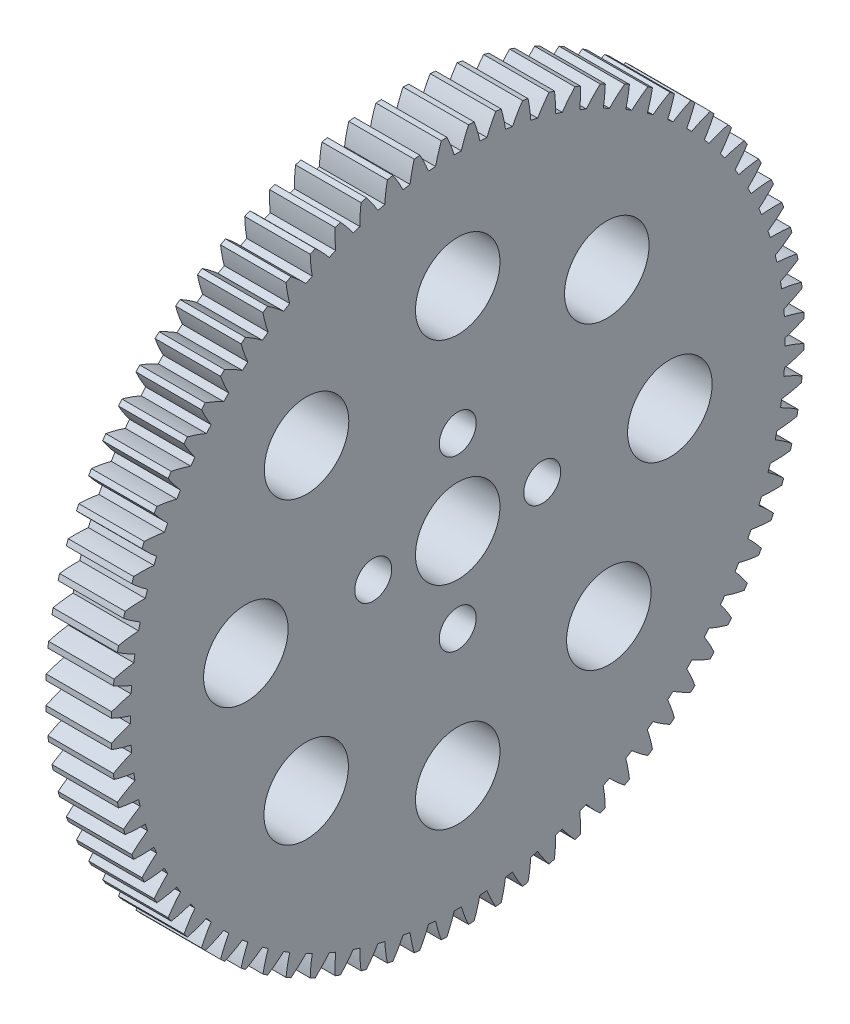
SolidWorks part; units mm, degrees
material "2024 Alloy"
ref_plane "Front Plane" through (0, 0, 0) normal (0, 0, 1) x (1, 0, 0)
ref_plane "Top Plane" through (0, 0, 0) normal (0, 1, 0) x (1, 0, 0)
ref_plane "Right Plane" through (0, 0, 0) normal (1, 0, 0) x (0, 0, -1)
ref_plane "Plane1" through (0, 0, 0) normal (-1, 0, 0) x (0, -1, 0)
sketch "Sketch1" plane through (0, 0, 0) normal (-1, 0, 0) x (0, -1, 0)
  circle A0 centre (0, 0) radius 4
  circle A1 centre (0, 8) radius 1.75
  circle A2 centre (-20.084, 0) radius 4
  circle A3 centre (20.0633, 0) radius 4
  circle A4 centre (0, -20.084) radius 4
  circle A5 centre (0, 20.0633) radius 4
  circle A6 centre (-14.3663, -14.1126) radius 4
  circle A7 centre (14.142, -14.3069) radius 4
  circle A8 centre (14.1351, 14.3483) radius 4
  circle A9 centre (-14.1597, 14.315) radius 4
  circle A10 centre (-8, 0) radius 1.75
  circle A11 centre (8, 0) radius 1.75
  circle A12 centre (0, -8) radius 1.75
  arc A13 (-32.5405, -4.1179) -> (-30.6681, -4.5175) centre (-28.9403, 8.1654) ccw
  arc A14 (-30.6681, -4.5175) -> (-30.563, -5.1806) centre (0, 0) ccw
  arc A15 (-30.563, -5.1806) -> (-32.2203, -6.1392) centre (-25.0006, -16.7088) ccw
  arc A16 (-32.2203, -6.1392) -> (-32.1171, -6.6583) centre (0, 0) ccw
  arc A17 (-32.1171, -6.6583) -> (-30.2191, -6.9097) centre (-29.4917, 5.8696) ccw
  arc A18 (-30.2191, -6.9097) -> (-30.0624, -7.5626) centre (0, 0) ccw
  arc A19 (-30.0624, -7.5626) -> (-31.6393, -8.6483) centre (-23.6126, -18.6188) ccw
  arc A20 (-31.6393, -8.6483) -> (-31.4957, -9.1576) centre (0, 0) ccw
  arc A21 (-31.4957, -9.1576) -> (-29.5838, -9.2594) centre (-29.8613, 3.5376) ccw
  arc A22 (-29.5838, -9.2594) -> (-29.3763, -9.8979) centre (0, 0) ccw
  arc A23 (-29.3763, -9.8979) -> (-30.8633, -11.104) centre (-22.079, -20.414) ccw
  arc A24 (-30.8633, -11.104) -> (-30.6801, -11.6005) centre (0, 0) ccw
  arc A25 (-30.6801, -11.6005) -> (-28.7661, -11.552) centre (-30.0469, 1.1838) ccw
  arc A26 (-28.7661, -11.552) -> (-28.5092, -12.1723) centre (0, 0) ccw
  arc A27 (-28.5092, -12.1723) -> (-29.8969, -13.4913) centre (-20.4093, -22.0834) ccw
  arc A28 (-29.8969, -13.4913) -> (-29.6753, -13.9719) centre (0, 0) ccw
  arc A29 (-29.6753, -13.9719) -> (-27.7711, -13.7733) centre (-30.0471, -1.1773) ccw
  arc A30 (-27.7711, -13.7733) -> (-27.4663, -14.3715) centre (0, 0) ccw
  arc A31 (-27.4663, -14.3715) -> (-28.7462, -15.7954) centre (-18.6137, -23.6166) ccw
  arc A32 (-28.7462, -15.7954) -> (-28.4876, -16.2571) centre (0, 0) ccw
  arc A33 (-28.4876, -16.2571) -> (-26.6048, -15.9097) centre (-29.8621, -3.5311) ccw
  arc A34 (-26.6048, -15.9097) -> (-26.254, -16.4822) centre (0, 0) ccw
  arc A35 (-26.254, -16.4822) -> (-27.4183, -18.0021) centre (-16.7034, -25.0042) ccw
  arc A36 (-27.4183, -18.0021) -> (-27.1243, -18.4421) centre (0, 0) ccw
  arc A37 (-27.1243, -18.4421) -> (-25.2746, -17.9481) centre (-29.493, -5.8632) ccw
  arc A38 (-25.2746, -17.9481) -> (-24.8799, -18.4913) centre (0, 0) ccw
  arc A39 (-24.8799, -18.4913) -> (-25.9214, -20.0978) centre (-14.6901, -26.2377) ccw
  arc A40 (-25.9214, -20.0978) -> (-25.5937, -20.5134) centre (0, 0) ccw
  arc A41 (-25.5937, -20.5134) -> (-23.7885, -19.8758) centre (-28.9421, -8.1591) ccw
  arc A42 (-23.7885, -19.8758) -> (-23.3524, -20.3863) centre (0, 0) ccw
  arc A43 (-23.3524, -20.3863) -> (-24.2646, -22.0696) centre (-12.5862, -27.3094) ccw
  arc A44 (-24.2646, -22.0696) -> (-23.9054, -22.4582) centre (0, 0) ccw
  arc A45 (-23.9054, -22.4582) -> (-22.1557, -21.6809) centre (-28.2127, -10.4047) ccw
  arc A46 (-22.1557, -21.6809) -> (-21.6809, -22.1557) centre (0, 0) ccw
  arc A47 (-21.6809, -22.1557) -> (-22.4582, -23.9054) centre (-10.4047, -28.2127) ccw
  arc A48 (-22.4582, -23.9054) -> (-22.0696, -24.2646) centre (0, 0) ccw
  arc A49 (-22.0696, -24.2646) -> (-20.3863, -23.3524) centre (-27.3094, -12.5862) ccw
  arc A50 (-20.3863, -23.3524) -> (-19.8758, -23.7885) centre (0, 0) ccw
  arc A51 (-19.8758, -23.7885) -> (-20.5134, -25.5937) centre (-8.1591, -28.9421) ccw
  arc A52 (-20.5134, -25.5937) -> (-20.0978, -25.9214) centre (0, 0) ccw
  arc A53 (-20.0978, -25.9214) -> (-18.4913, -24.8799) centre (-26.2377, -14.6901) ccw
  arc A54 (-18.4913, -24.8799) -> (-17.9481, -25.2746) centre (0, 0) ccw
  arc A55 (-17.9481, -25.2746) -> (-18.4421, -27.1243) centre (-5.8632, -29.493) ccw
  arc A56 (-18.4421, -27.1243) -> (-18.0021, -27.4183) centre (0, 0) ccw
  arc A57 (-18.0021, -27.4183) -> (-16.4822, -26.254) centre (-25.0042, -16.7034) ccw
  arc A58 (-16.4822, -26.254) -> (-15.9097, -26.6048) centre (0, 0) ccw
  arc A59 (-15.9097, -26.6048) -> (-16.2571, -28.4876) centre (-3.5311, -29.8621) ccw
  arc A60 (-16.2571, -28.4876) -> (-15.7954, -28.7462) centre (0, 0) ccw
  arc A61 (-15.7954, -28.7462) -> (-14.3715, -27.4663) centre (-23.6166, -18.6137) ccw
  arc A62 (-14.3715, -27.4663) -> (-13.7733, -27.7711) centre (0, 0) ccw
  arc A63 (-13.7733, -27.7711) -> (-13.9719, -29.6753) centre (-1.1773, -30.0471) ccw
  arc A64 (-13.9719, -29.6753) -> (-13.4913, -29.8969) centre (0, 0) ccw
  arc A65 (-13.4913, -29.8969) -> (-12.1723, -28.5092) centre (-22.0834, -20.4093) ccw
  arc A66 (-12.1723, -28.5092) -> (-11.552, -28.7661) centre (0, 0) ccw
  arc A67 (-11.552, -28.7661) -> (-11.6005, -30.6801) centre (1.1838, -30.0469) ccw
  arc A68 (-11.6005, -30.6801) -> (-11.104, -30.8633) centre (0, 0) ccw
  arc A69 (-11.104, -30.8633) -> (-9.8979, -29.3763) centre (-20.414, -22.079) ccw
  arc A70 (-9.8979, -29.3763) -> (-9.2594, -29.5838) centre (0, 0) ccw
  arc A71 (-9.2594, -29.5838) -> (-9.1576, -31.4957) centre (3.5376, -29.8613) ccw
  arc A72 (-9.1576, -31.4957) -> (-8.6483, -31.6393) centre (0, 0) ccw
  arc A73 (-8.6483, -31.6393) -> (-7.5626, -30.0624) centre (-18.6188, -23.6126) ccw
  arc A74 (-7.5626, -30.0624) -> (-6.9097, -30.2191) centre (0, 0) ccw
  arc A75 (-6.9097, -30.2191) -> (-6.6583, -32.1171) centre (5.8696, -29.4917) ccw
  arc A76 (-6.6583, -32.1171) -> (-6.1392, -32.2203) centre (0, 0) ccw
  arc A77 (-6.1392, -32.2203) -> (-5.1806, -30.563) centre (-16.7088, -25.0006) ccw
  arc A78 (-5.1806, -30.563) -> (-4.5175, -30.6681) centre (0, 0) ccw
  arc A79 (-4.5175, -30.6681) -> (-4.1179, -32.5405) centre (8.1654, -28.9403) ccw
  arc A80 (-4.1179, -32.5405) -> (-3.5923, -32.6027) centre (0, 0) ccw
  arc A81 (-3.5923, -32.6027) -> (-2.7667, -30.8753) centre (-14.6958, -26.2345) ccw
  arc A82 (-2.7667, -30.8753) -> (-2.0973, -30.928) centre (0, 0) ccw
  arc A83 (-2.0973, -30.928) -> (-1.5521, -32.7633) centre (10.4109, -28.2104) ccw
  arc A84 (-1.5521, -32.7633) -> (-1.0233, -32.784) centre (0, 0) ccw
  arc A85 (-1.0233, -32.784) -> (-0.3357, -30.9972) centre (-12.5921, -27.3066) ccw
  arc A86 (-0.3357, -30.9972) -> (0.3357, -30.9972) centre (0, 0) ccw
  arc A87 (0.3357, -30.9972) -> (1.0233, -32.784) centre (12.5921, -27.3066) ccw
  arc A88 (1.0233, -32.784) -> (1.5521, -32.7633) centre (0, 0) ccw
  arc A89 (1.5521, -32.7633) -> (2.0973, -30.928) centre (-10.4109, -28.2104) ccw
  arc A90 (2.0973, -30.928) -> (2.7667, -30.8753) centre (0, 0) ccw
  arc A91 (2.7667, -30.8753) -> (3.5923, -32.6027) centre (14.6958, -26.2345) ccw
  arc A92 (3.5923, -32.6027) -> (4.1179, -32.5405) centre (0, 0) ccw
  arc A93 (4.1179, -32.5405) -> (4.5175, -30.6681) centre (-8.1654, -28.9403) ccw
  arc A94 (4.5175, -30.6681) -> (5.1806, -30.563) centre (0, 0) ccw
  arc A95 (5.1806, -30.563) -> (6.1392, -32.2203) centre (16.7088, -25.0006) ccw
  arc A96 (6.1392, -32.2203) -> (6.6583, -32.1171) centre (0, 0) ccw
  arc A97 (6.6583, -32.1171) -> (6.9097, -30.2191) centre (-5.8696, -29.4917) ccw
  arc A98 (6.9097, -30.2191) -> (7.5626, -30.0624) centre (0, 0) ccw
  arc A99 (7.5626, -30.0624) -> (8.6483, -31.6393) centre (18.6188, -23.6126) ccw
  arc A100 (8.6483, -31.6393) -> (9.1576, -31.4957) centre (0, 0) ccw
  arc A101 (9.1576, -31.4957) -> (9.2594, -29.5838) centre (-3.5376, -29.8613) ccw
  arc A102 (9.2594, -29.5838) -> (9.8979, -29.3763) centre (0, 0) ccw
  arc A103 (9.8979, -29.3763) -> (11.104, -30.8633) centre (20.414, -22.079) ccw
  arc A104 (11.104, -30.8633) -> (11.6005, -30.6801) centre (0, 0) ccw
  arc A105 (11.6005, -30.6801) -> (11.552, -28.7661) centre (-1.1838, -30.0469) ccw
  arc A106 (11.552, -28.7661) -> (12.1723, -28.5092) centre (0, 0) ccw
  arc A107 (12.1723, -28.5092) -> (13.4913, -29.8969) centre (22.0834, -20.4093) ccw
  arc A108 (13.4913, -29.8969) -> (13.9719, -29.6753) centre (0, 0) ccw
  arc A109 (13.9719, -29.6753) -> (13.7733, -27.7711) centre (1.1773, -30.0471) ccw
  arc A110 (13.7733, -27.7711) -> (14.3715, -27.4663) centre (0, 0) ccw
  arc A111 (14.3715, -27.4663) -> (15.7954, -28.7462) centre (23.6166, -18.6137) ccw
  arc A112 (15.7954, -28.7462) -> (16.2571, -28.4876) centre (0, 0) ccw
  arc A113 (16.2571, -28.4876) -> (15.9097, -26.6048) centre (3.5311, -29.8621) ccw
  arc A114 (15.9097, -26.6048) -> (16.4822, -26.254) centre (0, 0) ccw
  arc A115 (16.4822, -26.254) -> (18.0021, -27.4183) centre (25.0042, -16.7034) ccw
  arc A116 (18.0021, -27.4183) -> (18.4421, -27.1243) centre (0, 0) ccw
  arc A117 (18.4421, -27.1243) -> (17.9481, -25.2746) centre (5.8632, -29.493) ccw
  arc A118 (17.9481, -25.2746) -> (18.4913, -24.8799) centre (0, 0) ccw
  arc A119 (18.4913, -24.8799) -> (20.0978, -25.9214) centre (26.2377, -14.6901) ccw
  arc A120 (20.0978, -25.9214) -> (20.5134, -25.5937) centre (0, 0) ccw
  arc A121 (20.5134, -25.5937) -> (19.8758, -23.7885) centre (8.1591, -28.9421) ccw
  arc A122 (19.8758, -23.7885) -> (20.3863, -23.3524) centre (0, 0) ccw
  arc A123 (20.3863, -23.3524) -> (22.0696, -24.2646) centre (27.3094, -12.5862) ccw
  arc A124 (22.0696, -24.2646) -> (22.4582, -23.9054) centre (0, 0) ccw
  arc A125 (22.4582, -23.9054) -> (21.6809, -22.1557) centre (10.4047, -28.2127) ccw
  arc A126 (21.6809, -22.1557) -> (22.1557, -21.6809) centre (0, 0) ccw
  arc A127 (22.1557, -21.6809) -> (23.9054, -22.4582) centre (28.2127, -10.4047) ccw
  arc A128 (23.9054, -22.4582) -> (24.2646, -22.0696) centre (0, 0) ccw
  arc A129 (24.2646, -22.0696) -> (23.3524, -20.3863) centre (12.5862, -27.3094) ccw
  arc A130 (23.3524, -20.3863) -> (23.7885, -19.8758) centre (0, 0) ccw
  arc A131 (23.7885, -19.8758) -> (25.5937, -20.5134) centre (28.9421, -8.1591) ccw
  arc A132 (25.5937, -20.5134) -> (25.9214, -20.0978) centre (0, 0) ccw
  arc A133 (25.9214, -20.0978) -> (24.8799, -18.4913) centre (14.6901, -26.2377) ccw
  arc A134 (24.8799, -18.4913) -> (25.2746, -17.9481) centre (0, 0) ccw
  arc A135 (25.2746, -17.9481) -> (27.1243, -18.4421) centre (29.493, -5.8632) ccw
  arc A136 (27.1243, -18.4421) -> (27.4183, -18.0021) centre (0, 0) ccw
  arc A137 (27.4183, -18.0021) -> (26.254, -16.4822) centre (16.7034, -25.0042) ccw
  arc A138 (26.254, -16.4822) -> (26.6048, -15.9097) centre (0, 0) ccw
  arc A139 (26.6048, -15.9097) -> (28.4876, -16.2571) centre (29.8621, -3.5311) ccw
  arc A140 (28.4876, -16.2571) -> (28.7462, -15.7954) centre (0, 0) ccw
  arc A141 (28.7462, -15.7954) -> (27.4663, -14.3715) centre (18.6137, -23.6166) ccw
  arc A142 (27.4663, -14.3715) -> (27.7711, -13.7733) centre (0, 0) ccw
  arc A143 (27.7711, -13.7733) -> (29.6753, -13.9719) centre (30.0471, -1.1773) ccw
  arc A144 (29.6753, -13.9719) -> (29.8969, -13.4913) centre (0, 0) ccw
  arc A145 (29.8969, -13.4913) -> (28.5092, -12.1723) centre (20.4093, -22.0834) ccw
  arc A146 (28.5092, -12.1723) -> (28.7661, -11.552) centre (0, 0) ccw
  arc A147 (28.7661, -11.552) -> (30.6801, -11.6005) centre (30.0469, 1.1838) ccw
  arc A148 (30.6801, -11.6005) -> (30.8633, -11.104) centre (0, 0) ccw
  arc A149 (30.8633, -11.104) -> (29.3763, -9.8979) centre (22.079, -20.414) ccw
  arc A150 (29.3763, -9.8979) -> (29.5838, -9.2594) centre (0, 0) ccw
  arc A151 (29.5838, -9.2594) -> (31.4957, -9.1576) centre (29.8613, 3.5376) ccw
  arc A152 (31.4957, -9.1576) -> (31.6393, -8.6483) centre (0, 0) ccw
  arc A153 (31.6393, -8.6483) -> (30.0624, -7.5626) centre (23.6126, -18.6188) ccw
  arc A154 (30.0624, -7.5626) -> (30.2191, -6.9097) centre (0, 0) ccw
  arc A155 (30.2191, -6.9097) -> (32.1171, -6.6583) centre (29.4917, 5.8696) ccw
  arc A156 (32.1171, -6.6583) -> (32.2203, -6.1392) centre (0, 0) ccw
  arc A157 (32.2203, -6.1392) -> (30.563, -5.1806) centre (25.0006, -16.7088) ccw
  arc A158 (30.563, -5.1806) -> (30.6681, -4.5175) centre (0, 0) ccw
  arc A159 (30.6681, -4.5175) -> (32.5405, -4.1179) centre (28.9403, 8.1654) ccw
  arc A160 (32.5405, -4.1179) -> (32.6027, -3.5923) centre (0, 0) ccw
  arc A161 (32.6027, -3.5923) -> (30.8753, -2.7667) centre (26.2345, -14.6958) ccw
  arc A162 (30.8753, -2.7667) -> (30.928, -2.0973) centre (0, 0) ccw
  arc A163 (30.928, -2.0973) -> (32.7633, -1.5521) centre (28.2104, 10.4109) ccw
  arc A164 (32.7633, -1.5521) -> (32.784, -1.0233) centre (0, 0) ccw
  arc A165 (32.784, -1.0233) -> (30.9972, -0.3357) centre (27.3066, -12.5921) ccw
  arc A166 (30.9972, -0.3357) -> (30.9972, 0.3357) centre (0, 0) ccw
  arc A167 (30.9972, 0.3357) -> (32.784, 1.0233) centre (27.3066, 12.5921) ccw
  arc A168 (32.784, 1.0233) -> (32.7633, 1.5521) centre (0, 0) ccw
  arc A169 (32.7633, 1.5521) -> (30.928, 2.0973) centre (28.2104, -10.4109) ccw
  arc A170 (30.928, 2.0973) -> (30.8753, 2.7667) centre (0, 0) ccw
  arc A171 (30.8753, 2.7667) -> (32.6027, 3.5923) centre (26.2345, 14.6958) ccw
  arc A172 (32.6027, 3.5923) -> (32.5405, 4.1179) centre (0, 0) ccw
  arc A173 (32.5405, 4.1179) -> (30.6681, 4.5175) centre (28.9403, -8.1654) ccw
  arc A174 (30.6681, 4.5175) -> (30.563, 5.1806) centre (0, 0) ccw
  arc A175 (30.563, 5.1806) -> (32.2203, 6.1392) centre (25.0006, 16.7088) ccw
  arc A176 (32.2203, 6.1392) -> (32.1171, 6.6583) centre (0, 0) ccw
  arc A177 (32.1171, 6.6583) -> (30.2191, 6.9097) centre (29.4917, -5.8696) ccw
  arc A178 (30.2191, 6.9097) -> (30.0624, 7.5626) centre (0, 0) ccw
  arc A179 (30.0624, 7.5626) -> (31.6393, 8.6483) centre (23.6126, 18.6188) ccw
  arc A180 (31.6393, 8.6483) -> (31.4957, 9.1576) centre (0, 0) ccw
  arc A181 (31.4957, 9.1576) -> (29.5838, 9.2594) centre (29.8613, -3.5376) ccw
  arc A182 (29.5838, 9.2594) -> (29.3763, 9.8979) centre (0, 0) ccw
  arc A183 (29.3763, 9.8979) -> (30.8633, 11.104) centre (22.079, 20.414) ccw
  arc A184 (30.8633, 11.104) -> (30.6801, 11.6005) centre (0, 0) ccw
  arc A185 (30.6801, 11.6005) -> (28.7661, 11.552) centre (30.0469, -1.1838) ccw
  arc A186 (28.7661, 11.552) -> (28.5092, 12.1723) centre (0, 0) ccw
  arc A187 (28.5092, 12.1723) -> (29.8969, 13.4913) centre (20.4093, 22.0834) ccw
  arc A188 (29.8969, 13.4913) -> (29.6753, 13.9719) centre (0, 0) ccw
  arc A189 (29.6753, 13.9719) -> (27.7711, 13.7733) centre (30.0471, 1.1773) ccw
  arc A190 (27.7711, 13.7733) -> (27.4663, 14.3715) centre (0, 0) ccw
  arc A191 (27.4663, 14.3715) -> (28.7462, 15.7954) centre (18.6137, 23.6166) ccw
  arc A192 (28.7462, 15.7954) -> (28.4876, 16.2571) centre (0, 0) ccw
  arc A193 (28.4876, 16.2571) -> (26.6048, 15.9097) centre (29.8621, 3.5311) ccw
  arc A194 (26.6048, 15.9097) -> (26.254, 16.4822) centre (0, 0) ccw
  arc A195 (26.254, 16.4822) -> (27.4183, 18.0021) centre (16.7034, 25.0042) ccw
  arc A196 (27.4183, 18.0021) -> (27.1243, 18.4421) centre (0, 0) ccw
  arc A197 (27.1243, 18.4421) -> (25.2746, 17.9481) centre (29.493, 5.8632) ccw
  arc A198 (25.2746, 17.9481) -> (24.8799, 18.4913) centre (0, 0) ccw
  arc A199 (24.8799, 18.4913) -> (25.9214, 20.0978) centre (14.6901, 26.2377) ccw
  arc A200 (25.9214, 20.0978) -> (25.5937, 20.5134) centre (0, 0) ccw
  arc A201 (25.5937, 20.5134) -> (23.7885, 19.8758) centre (28.9421, 8.1591) ccw
  arc A202 (23.7885, 19.8758) -> (23.3524, 20.3863) centre (0, 0) ccw
  arc A203 (23.3524, 20.3863) -> (24.2646, 22.0696) centre (12.5862, 27.3094) ccw
  arc A204 (24.2646, 22.0696) -> (23.9054, 22.4582) centre (0, 0) ccw
  arc A205 (23.9054, 22.4582) -> (22.1557, 21.6809) centre (28.2127, 10.4047) ccw
  arc A206 (22.1557, 21.6809) -> (21.6809, 22.1557) centre (0, 0) ccw
  arc A207 (21.6809, 22.1557) -> (22.4582, 23.9054) centre (10.4047, 28.2127) ccw
  arc A208 (22.4582, 23.9054) -> (22.0696, 24.2646) centre (0, 0) ccw
  arc A209 (22.0696, 24.2646) -> (20.3863, 23.3524) centre (27.3094, 12.5862) ccw
  arc A210 (20.3863, 23.3524) -> (19.8758, 23.7885) centre (0, 0) ccw
  arc A211 (19.8758, 23.7885) -> (20.5134, 25.5937) centre (8.1591, 28.9421) ccw
  arc A212 (20.5134, 25.5937) -> (20.0978, 25.9214) centre (0, 0) ccw
  arc A213 (20.0978, 25.9214) -> (18.4913, 24.8799) centre (26.2377, 14.6901) ccw
  arc A214 (18.4913, 24.8799) -> (17.9481, 25.2746) centre (0, 0) ccw
  arc A215 (17.9481, 25.2746) -> (18.4421, 27.1243) centre (5.8632, 29.493) ccw
  arc A216 (18.4421, 27.1243) -> (18.0021, 27.4183) centre (0, 0) ccw
  arc A217 (18.0021, 27.4183) -> (16.4822, 26.254) centre (25.0042, 16.7034) ccw
  arc A218 (16.4822, 26.254) -> (15.9097, 26.6048) centre (0, 0) ccw
  arc A219 (15.9097, 26.6048) -> (16.2571, 28.4876) centre (3.5311, 29.8621) ccw
  arc A220 (16.2571, 28.4876) -> (15.7954, 28.7462) centre (0, 0) ccw
  arc A221 (15.7954, 28.7462) -> (14.3715, 27.4663) centre (23.6166, 18.6137) ccw
  arc A222 (14.3715, 27.4663) -> (13.7733, 27.7711) centre (0, 0) ccw
  arc A223 (13.7733, 27.7711) -> (13.9719, 29.6753) centre (1.1773, 30.0471) ccw
  arc A224 (13.9719, 29.6753) -> (13.4913, 29.8969) centre (0, 0) ccw
  arc A225 (13.4913, 29.8969) -> (12.1723, 28.5092) centre (22.0834, 20.4093) ccw
  arc A226 (12.1723, 28.5092) -> (11.552, 28.7661) centre (0, 0) ccw
  arc A227 (11.552, 28.7661) -> (11.6005, 30.6801) centre (-1.1838, 30.0469) ccw
  arc A228 (11.6005, 30.6801) -> (11.104, 30.8633) centre (0, 0) ccw
  arc A229 (11.104, 30.8633) -> (9.8979, 29.3763) centre (20.414, 22.079) ccw
  arc A230 (9.8979, 29.3763) -> (9.2594, 29.5838) centre (0, 0) ccw
  arc A231 (9.2594, 29.5838) -> (9.1576, 31.4957) centre (-3.5376, 29.8613) ccw
  arc A232 (9.1576, 31.4957) -> (8.6483, 31.6393) centre (0, 0) ccw
  arc A233 (8.6483, 31.6393) -> (7.5626, 30.0624) centre (18.6188, 23.6126) ccw
  arc A234 (7.5626, 30.0624) -> (6.9097, 30.2191) centre (0, 0) ccw
  arc A235 (6.9097, 30.2191) -> (6.6583, 32.1171) centre (-5.8696, 29.4917) ccw
  arc A236 (6.6583, 32.1171) -> (6.1392, 32.2203) centre (0, 0) ccw
  arc A237 (6.1392, 32.2203) -> (5.1806, 30.563) centre (16.7088, 25.0006) ccw
  arc A238 (5.1806, 30.563) -> (4.5175, 30.6681) centre (0, 0) ccw
  arc A239 (4.5175, 30.6681) -> (4.1179, 32.5405) centre (-8.1654, 28.9403) ccw
  arc A240 (4.1179, 32.5405) -> (3.5923, 32.6027) centre (0, 0) ccw
  arc A241 (3.5923, 32.6027) -> (2.7667, 30.8753) centre (14.6958, 26.2345) ccw
  arc A242 (2.7667, 30.8753) -> (2.0973, 30.928) centre (0, 0) ccw
  arc A243 (2.0973, 30.928) -> (1.5521, 32.7633) centre (-10.4109, 28.2104) ccw
  arc A244 (1.5521, 32.7633) -> (1.0233, 32.784) centre (0, 0) ccw
  arc A245 (1.0233, 32.784) -> (0.3357, 30.9972) centre (12.5921, 27.3066) ccw
  arc A246 (0.3357, 30.9972) -> (-0.3357, 30.9972) centre (0, 0) ccw
  arc A247 (-0.3357, 30.9972) -> (-1.0233, 32.784) centre (-12.5921, 27.3066) ccw
  arc A248 (-1.0233, 32.784) -> (-1.5521, 32.7633) centre (0, 0) ccw
  arc A249 (-1.5521, 32.7633) -> (-2.0973, 30.928) centre (10.4109, 28.2104) ccw
  arc A250 (-2.0973, 30.928) -> (-2.7667, 30.8753) centre (0, 0) ccw
  arc A251 (-2.7667, 30.8753) -> (-3.5923, 32.6027) centre (-14.6958, 26.2345) ccw
  arc A252 (-3.5923, 32.6027) -> (-4.1179, 32.5405) centre (0, 0) ccw
  arc A253 (-4.1179, 32.5405) -> (-4.5175, 30.6681) centre (8.1654, 28.9403) ccw
  arc A254 (-4.5175, 30.6681) -> (-5.1806, 30.563) centre (0, 0) ccw
  arc A255 (-5.1806, 30.563) -> (-6.1392, 32.2203) centre (-16.7088, 25.0006) ccw
  arc A256 (-6.1392, 32.2203) -> (-6.6583, 32.1171) centre (0, 0) ccw
  arc A257 (-6.6583, 32.1171) -> (-6.9097, 30.2191) centre (5.8696, 29.4917) ccw
  arc A258 (-6.9097, 30.2191) -> (-7.5626, 30.0624) centre (0, 0) ccw
  arc A259 (-7.5626, 30.0624) -> (-8.6483, 31.6393) centre (-18.6188, 23.6126) ccw
  arc A260 (-8.6483, 31.6393) -> (-9.1576, 31.4957) centre (0, 0) ccw
  arc A261 (-9.1576, 31.4957) -> (-9.2594, 29.5838) centre (3.5376, 29.8613) ccw
  arc A262 (-9.2594, 29.5838) -> (-9.8979, 29.3763) centre (0, 0) ccw
  arc A263 (-9.8979, 29.3763) -> (-11.104, 30.8633) centre (-20.414, 22.079) ccw
  arc A264 (-11.104, 30.8633) -> (-11.6005, 30.6801) centre (0, 0) ccw
  arc A265 (-11.6005, 30.6801) -> (-11.552, 28.7661) centre (1.1838, 30.0469) ccw
  arc A266 (-11.552, 28.7661) -> (-12.1723, 28.5092) centre (0, 0) ccw
  arc A267 (-12.1723, 28.5092) -> (-13.4913, 29.8969) centre (-22.0834, 20.4093) ccw
  arc A268 (-13.4913, 29.8969) -> (-13.9719, 29.6753) centre (0, 0) ccw
  arc A269 (-13.9719, 29.6753) -> (-13.7733, 27.7711) centre (-1.1773, 30.0471) ccw
  arc A270 (-13.7733, 27.7711) -> (-14.3715, 27.4663) centre (0, 0) ccw
  arc A271 (-14.3715, 27.4663) -> (-15.7954, 28.7462) centre (-23.6166, 18.6137) ccw
  arc A272 (-15.7954, 28.7462) -> (-16.2571, 28.4876) centre (0, 0) ccw
  arc A273 (-16.2571, 28.4876) -> (-15.9097, 26.6048) centre (-3.5311, 29.8621) ccw
  arc A274 (-15.9097, 26.6048) -> (-16.4822, 26.254) centre (0, 0) ccw
  arc A275 (-16.4822, 26.254) -> (-18.0021, 27.4183) centre (-25.0042, 16.7034) ccw
  arc A276 (-18.0021, 27.4183) -> (-18.4421, 27.1243) centre (0, 0) ccw
  arc A277 (-18.4421, 27.1243) -> (-17.9481, 25.2746) centre (-5.8632, 29.493) ccw
  arc A278 (-17.9481, 25.2746) -> (-18.4913, 24.8799) centre (0, 0) ccw
  arc A279 (-18.4913, 24.8799) -> (-20.0978, 25.9214) centre (-26.2377, 14.6901) ccw
  arc A280 (-20.0978, 25.9214) -> (-20.5134, 25.5937) centre (0, 0) ccw
  arc A281 (-20.5134, 25.5937) -> (-19.8758, 23.7885) centre (-8.1591, 28.9421) ccw
  arc A282 (-19.8758, 23.7885) -> (-20.3863, 23.3524) centre (0, 0) ccw
  arc A283 (-20.3863, 23.3524) -> (-22.0696, 24.2646) centre (-27.3094, 12.5862) ccw
  arc A284 (-22.0696, 24.2646) -> (-22.4582, 23.9054) centre (0, 0) ccw
  arc A285 (-22.4582, 23.9054) -> (-21.6809, 22.1557) centre (-10.4047, 28.2127) ccw
  arc A286 (-21.6809, 22.1557) -> (-22.1557, 21.6809) centre (0, 0) ccw
  arc A287 (-22.1557, 21.6809) -> (-23.9054, 22.4582) centre (-28.2127, 10.4047) ccw
  arc A288 (-23.9054, 22.4582) -> (-24.2646, 22.0696) centre (0, 0) ccw
  arc A289 (-24.2646, 22.0696) -> (-23.3524, 20.3863) centre (-12.5862, 27.3094) ccw
  arc A290 (-23.3524, 20.3863) -> (-23.7885, 19.8758) centre (0, 0) ccw
  arc A291 (-23.7885, 19.8758) -> (-25.5937, 20.5134) centre (-28.9421, 8.1591) ccw
  arc A292 (-25.5937, 20.5134) -> (-25.9214, 20.0978) centre (0, 0) ccw
  arc A293 (-25.9214, 20.0978) -> (-24.8799, 18.4913) centre (-14.6901, 26.2377) ccw
  arc A294 (-24.8799, 18.4913) -> (-25.2746, 17.9481) centre (0, 0) ccw
  arc A295 (-25.2746, 17.9481) -> (-27.1243, 18.4421) centre (-29.493, 5.8632) ccw
  arc A296 (-27.1243, 18.4421) -> (-27.4183, 18.0021) centre (0, 0) ccw
  arc A297 (-27.4183, 18.0021) -> (-26.254, 16.4822) centre (-16.7034, 25.0042) ccw
  arc A298 (-26.254, 16.4822) -> (-26.6048, 15.9097) centre (0, 0) ccw
  arc A299 (-26.6048, 15.9097) -> (-28.4876, 16.2571) centre (-29.8621, 3.5311) ccw
  arc A300 (-28.4876, 16.2571) -> (-28.7462, 15.7954) centre (0, 0) ccw
  arc A301 (-28.7462, 15.7954) -> (-27.4663, 14.3715) centre (-18.6137, 23.6166) ccw
  arc A302 (-27.4663, 14.3715) -> (-27.7711, 13.7733) centre (0, 0) ccw
  arc A303 (-27.7711, 13.7733) -> (-29.6753, 13.9719) centre (-30.0471, 1.1773) ccw
  arc A304 (-29.6753, 13.9719) -> (-29.8969, 13.4913) centre (0, 0) ccw
  arc A305 (-29.8969, 13.4913) -> (-28.5092, 12.1723) centre (-20.4093, 22.0834) ccw
  arc A306 (-28.5092, 12.1723) -> (-28.7661, 11.552) centre (0, 0) ccw
  arc A307 (-28.7661, 11.552) -> (-30.6801, 11.6005) centre (-30.0469, -1.1838) ccw
  arc A308 (-30.6801, 11.6005) -> (-30.8633, 11.104) centre (0, 0) ccw
  arc A309 (-30.8633, 11.104) -> (-29.3763, 9.8979) centre (-22.079, 20.414) ccw
  arc A310 (-29.3763, 9.8979) -> (-29.5838, 9.2594) centre (0, 0) ccw
  arc A311 (-29.5838, 9.2594) -> (-31.4957, 9.1576) centre (-29.8613, -3.5376) ccw
  arc A312 (-31.4957, 9.1576) -> (-31.6393, 8.6483) centre (0, 0) ccw
  arc A313 (-31.6393, 8.6483) -> (-30.0624, 7.5626) centre (-23.6126, 18.6188) ccw
  arc A314 (-30.0624, 7.5626) -> (-30.2191, 6.9097) centre (0, 0) ccw
  arc A315 (-30.2191, 6.9097) -> (-32.1171, 6.6583) centre (-29.4917, -5.8696) ccw
  arc A316 (-32.1171, 6.6583) -> (-32.2203, 6.1392) centre (0, 0) ccw
  arc A317 (-32.2203, 6.1392) -> (-30.563, 5.1806) centre (-25.0006, 16.7088) ccw
  arc A318 (-30.563, 5.1806) -> (-30.6681, 4.5175) centre (0, 0) ccw
  arc A319 (-30.6681, 4.5175) -> (-32.5405, 4.1179) centre (-28.9403, -8.1654) ccw
  arc A320 (-32.5405, 4.1179) -> (-32.6027, 3.5923) centre (0, 0) ccw
  arc A321 (-32.6027, 3.5923) -> (-30.8753, 2.7667) centre (-26.2345, 14.6958) ccw
  arc A322 (-30.8753, 2.7667) -> (-30.928, 2.0973) centre (0, 0) ccw
  arc A323 (-30.928, 2.0973) -> (-32.7633, 1.5521) centre (-28.2104, -10.4109) ccw
  arc A324 (-32.7633, 1.5521) -> (-32.784, 1.0233) centre (0, 0) ccw
  arc A325 (-32.784, 1.0233) -> (-30.9972, 0.3357) centre (-27.3066, 12.5921) ccw
  arc A326 (-30.9972, 0.3357) -> (-30.9972, -0.3357) centre (0, 0) ccw
  arc A327 (-30.9972, -0.3357) -> (-32.784, -1.0233) centre (-27.3066, -12.5921) ccw
  arc A328 (-32.784, -1.0233) -> (-32.7633, -1.5521) centre (0, 0) ccw
  arc A329 (-32.7633, -1.5521) -> (-30.928, -2.0973) centre (-28.2104, 10.4109) ccw
  arc A330 (-30.928, -2.0973) -> (-30.8753, -2.7667) centre (0, 0) ccw
  arc A331 (-30.8753, -2.7667) -> (-32.6027, -3.5923) centre (-26.2345, -14.6958) ccw
  arc A332 (-32.6027, -3.5923) -> (-32.5405, -4.1179) centre (0, 0) ccw
extrude "Boss-Extrude1" add sketch "Sketch1" against normal blind 6.2
